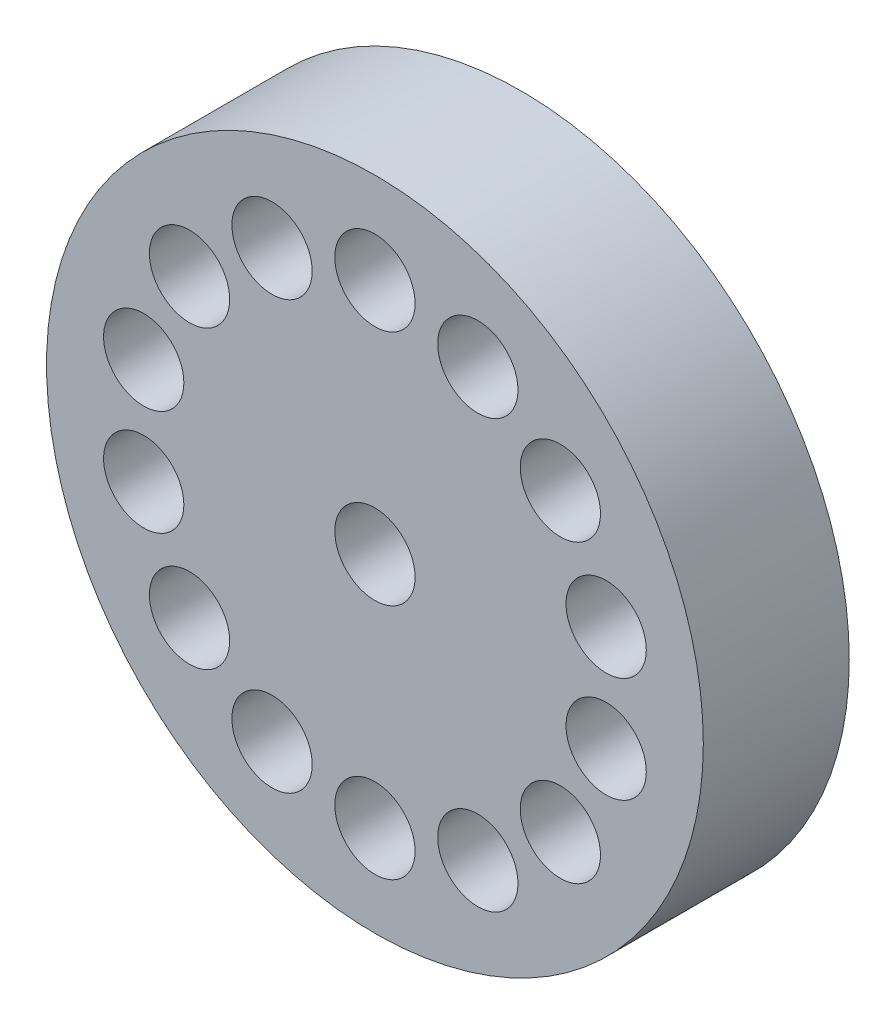
SolidWorks part; units mm, degrees
ref_plane "Płaszczyzna przednia" through (0, 0, 0) normal (0, 0, 1) x (1, 0, 0)
ref_plane "Płaszczyzna górna" through (0, 0, 0) normal (0, 1, 0) x (1, 0, 0)
ref_plane "Płaszczyzna prawa" through (0, 0, 0) normal (1, 0, 0) x (0, 0, -1)
sketch "Szkic1" plane through (0, 0, 0) normal (0, 0, 1) x (1, 0, 0)
  circle A0 centre (0, 0) radius 4.5
  circle A1 centre (0, 0) radius 0.55
  dimension "D1" = 9
  dimension "D2" = 1.1
extrude "Dodanie-wyciągnięcie1" add sketch "Szkic1" along normal blind 2
sketch "Szkic2" plane through (0, 0, 2) normal (0, 0, 1) x (1, 0, 0)
  circle A0 centre (0, 3.25) radius 0.55
  circle A1 centre (1.4101, 2.9281) radius 0.55
  circle A2 centre (2.541, 2.0263) radius 0.55
  circle A3 centre (3.1685, 0.7232) radius 0.55
  circle A4 centre (3.1685, -0.7232) radius 0.55
  circle A5 centre (2.541, -2.0263) radius 0.55
  circle A6 centre (1.4101, -2.9281) radius 0.55
  circle A7 centre (0, -3.25) radius 0.55
  circle A8 centre (-1.4101, -2.9281) radius 0.55
  circle A9 centre (-2.541, -2.0263) radius 0.55
  circle A10 centre (-3.1685, -0.7232) radius 0.55
  circle A11 centre (-3.1685, 0.7232) radius 0.55
  circle A12 centre (-2.541, 2.0263) radius 0.55
  circle A13 centre (-1.4101, 2.9281) radius 0.55
  point P31 (0, 0)
  dimension "D1" = 1.1
  dimension "D2" = 3.25
  dimension "D3" = 14
extrude "Wytnij-wyciągnięcie1" cut sketch "Szkic2" against normal blind 1
